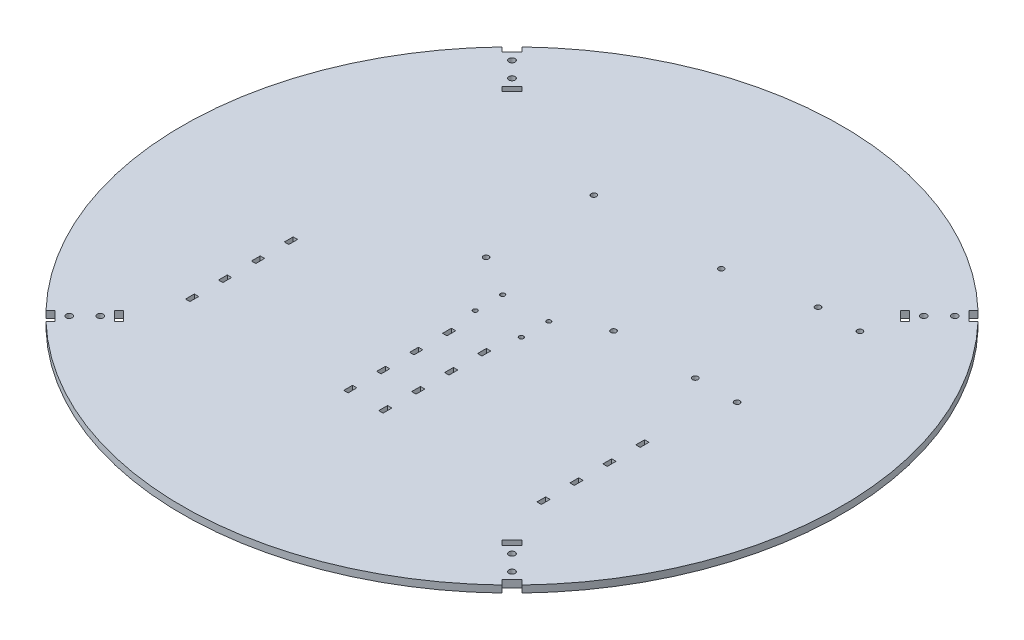
SolidWorks part; units mm, degrees
material "Acrylic (Medium-high impact)"
ref_plane "Front Plane" through (0, 0, 0) normal (0, 0, 1) x (1, 0, 0)
ref_plane "Top Plane" through (0, 0, 0) normal (0, 1, 0) x (1, 0, 0)
ref_plane "Right Plane" through (0, 0, 0) normal (1, 0, 0) x (0, 0, -1)
sketch "Sketch1" plane through (0, 0, 0) normal (0, 1, 0) x (1, 0, 0)
  line L0 (106.066, 212.132) -> (106.066, 0) construction
  line L5 (77.066, 172.2939) -> (135.066, 172.2939) construction
  line L6 (77.066, 172.2939) -> (77.066, 123.2939) construction
  line L7 (77.066, 123.2939) -> (135.066, 123.2939) construction
  line L8 (135.066, 172.2939) -> (135.066, 123.2939) construction
  line L9 (95.566, 99.816) -> (116.566, 99.816) construction
  line L10 (95.566, 99.816) -> (95.566, 112.316) construction
  line L11 (95.566, 112.316) -> (116.566, 112.316) construction
  line L12 (116.566, 99.816) -> (116.566, 112.316) construction
  line L13 (99.0985, 83.4399) -> (99.0985, 87.4399)
  line L14 (27.0985, 94.9399) -> (97.0985, 94.9399) construction
  line L15 (27.0985, 94.9399) -> (27.0985, 29.9399) construction
  line L16 (27.0985, 29.9399) -> (97.0985, 29.9399) construction
  line L17 (97.0985, 94.9399) -> (97.0985, 29.9399) construction
  line L18 (27.0985, 83.4399) -> (25.0985, 83.4399)
  line L19 (27.0985, 83.4399) -> (27.0985, 87.4399)
  line L20 (27.0985, 87.4399) -> (25.0985, 87.4399)
  line L21 (25.0985, 83.4399) -> (25.0985, 87.4399)
  line L22 (99.0985, 83.4399) -> (97.0985, 83.4399)
  line L23 (97.0985, 83.4399) -> (97.0985, 87.4399)
  line L24 (99.0985, 87.4399) -> (97.0985, 87.4399)
  line L25 (99.0985, 68.4399) -> (99.0985, 72.4399)
  line L26 (99.0985, 68.4399) -> (97.0985, 68.4399)
  line L27 (97.0985, 68.4399) -> (97.0985, 72.4399)
  line L28 (99.0985, 72.4399) -> (97.0985, 72.4399)
  line L29 (99.0985, 53.4399) -> (99.0985, 57.4399)
  line L30 (99.0985, 53.4399) -> (97.0985, 53.4399)
  line L31 (97.0985, 53.4399) -> (97.0985, 57.4399)
  line L32 (99.0985, 57.4399) -> (97.0985, 57.4399)
  line L33 (99.0985, 38.4399) -> (99.0985, 42.4399)
  line L34 (99.0985, 38.4399) -> (97.0985, 38.4399)
  line L35 (97.0985, 38.4399) -> (97.0985, 42.4399)
  line L36 (99.0985, 42.4399) -> (97.0985, 42.4399)
  line L37 (27.0985, 68.4399) -> (27.0985, 72.4399)
  line L38 (27.0985, 68.4399) -> (25.0985, 68.4399)
  line L39 (25.0985, 68.4399) -> (25.0985, 72.4399)
  line L40 (27.0985, 72.4399) -> (25.0985, 72.4399)
  line L41 (27.0985, 53.4399) -> (27.0985, 57.4399)
  line L42 (27.0985, 53.4399) -> (25.0985, 53.4399)
  line L43 (25.0985, 53.4399) -> (25.0985, 57.4399)
  line L44 (27.0985, 57.4399) -> (25.0985, 57.4399)
  line L45 (27.0985, 38.4399) -> (27.0985, 42.4399)
  line L46 (27.0985, 38.4399) -> (25.0985, 38.4399)
  line L47 (25.0985, 38.4399) -> (25.0985, 42.4399)
  line L48 (27.0985, 42.4399) -> (25.0985, 42.4399)
  line L49 (106.066, 112.316) -> (106.066, 99.816) construction
  line L50 (172.245, 123.2939) -> (172.245, 179.1739) construction
  line L51 (172.245, 123.2939) -> (191.295, 123.2939) construction
  line L52 (191.295, 123.2939) -> (191.295, 179.1739) construction
  line L53 (172.245, 179.1739) -> (191.295, 179.1739) construction
  line L54 (113.0335, 83.4399) -> (115.0335, 83.4399)
  line L55 (115.0335, 83.4399) -> (115.0335, 87.4399)
  line L56 (113.0335, 87.4399) -> (115.0335, 87.4399)
  line L57 (113.0335, 83.4399) -> (113.0335, 87.4399)
  line L58 (113.0335, 68.4399) -> (115.0335, 68.4399)
  line L59 (115.0335, 68.4399) -> (115.0335, 72.4399)
  line L60 (113.0335, 72.4399) -> (115.0335, 72.4399)
  line L61 (113.0335, 68.4399) -> (113.0335, 72.4399)
  line L62 (113.0335, 53.4399) -> (115.0335, 53.4399)
  line L63 (115.0335, 53.4399) -> (115.0335, 57.4399)
  line L64 (113.0335, 57.4399) -> (115.0335, 57.4399)
  line L65 (113.0335, 53.4399) -> (113.0335, 57.4399)
  line L66 (113.0335, 38.4399) -> (115.0335, 38.4399)
  line L67 (115.0335, 38.4399) -> (115.0335, 42.4399)
  line L68 (113.0335, 42.4399) -> (115.0335, 42.4399)
  line L69 (113.0335, 38.4399) -> (113.0335, 42.4399)
  line L70 (185.0335, 38.4399) -> (187.0335, 38.4399)
  line L71 (187.0335, 38.4399) -> (187.0335, 42.4399)
  line L72 (185.0335, 42.4399) -> (187.0335, 42.4399)
  line L73 (185.0335, 38.4399) -> (185.0335, 42.4399)
  line L74 (185.0335, 53.4399) -> (187.0335, 53.4399)
  line L75 (187.0335, 53.4399) -> (187.0335, 57.4399)
  line L76 (185.0335, 57.4399) -> (187.0335, 57.4399)
  line L77 (185.0335, 53.4399) -> (185.0335, 57.4399)
  line L78 (185.0335, 68.4399) -> (187.0335, 68.4399)
  line L79 (187.0335, 68.4399) -> (187.0335, 72.4399)
  line L80 (185.0335, 72.4399) -> (187.0335, 72.4399)
  line L81 (185.0335, 68.4399) -> (185.0335, 72.4399)
  line L82 (185.0335, 87.4399) -> (187.0335, 87.4399)
  line L83 (187.0335, 83.4399) -> (187.0335, 87.4399)
  line L84 (185.0335, 83.4399) -> (187.0335, 83.4399)
  line L85 (185.0335, 83.4399) -> (185.0335, 87.4399)
  circle A0 centre (77.066, 172.2939) radius 1.25
  circle A1 centre (135.066, 172.2939) radius 1.25
  circle A2 centre (77.066, 123.2939) radius 1.25
  circle A3 centre (135.066, 123.2939) radius 1.25
  circle A6 centre (95.566, 112.316) radius 1
  circle A7 centre (116.566, 112.316) radius 1
  circle A8 centre (116.566, 99.816) radius 1
  circle A9 centre (95.566, 99.816) radius 1
  circle A10 centre (172.245, 123.2939) radius 1.25
  circle A11 centre (172.245, 179.1739) radius 1.25
  circle A12 centre (191.295, 123.2939) radius 1.25
  circle A13 centre (191.295, 179.1739) radius 1.25
  circle A14 centre (106.066, 106.066) radius 150
  point P15 (106.066, 172.2939)
  point P78 (106.066, 106.066)
  point P92 (80, 80)
  dimension "D3" = 2.5
  dimension "D4" = 300
  dimension "D11" = 2
  dimension "D23" = 2.5
  dimension "D1" = 58
  dimension "D2" = 49
  dimension "D9" = 21
  dimension "D10" = 12.5
  dimension "D13" = 70
  dimension "D14" = 65
  dimension "D16" = 2
  dimension "D17" = 4
  dimension "D18" = 7.5
  dimension "D21" = 55.88
  dimension "D22" = 19.05
  dimension "D19" = 2
  dimension "D20" = 4
extrude "Boss-Extrude1" add sketch "Sketch1" along normal blind 3.175
sketch "Sketch2" plane through (0, 3.175, 0) normal (0, 1, 0) x (1, 0, 0)
  line L0 (15.4326, 192.2093) -> (13.3113, 194.3306) construction
  line L1 (13.3113, 194.3306) -> (17.8014, 198.8207) construction
  line L2 (17.8014, 198.8207) -> (19.9227, 196.6994) construction
  line L3 (19.9227, 196.6994) -> (15.4326, 192.2093) construction
  line L4 (-0.1237, 207.7656) -> (-2.2451, 209.887) construction
  line L5 (-2.2451, 209.887) -> (2.2451, 214.3771) construction
  line L6 (2.2451, 214.3771) -> (4.3664, 212.2558) construction
  line L7 (4.3664, 212.2558) -> (-0.1237, 207.7656) construction
  line L8 (15.4326, 192.2093) -> (13.3113, 194.3306)
  line L9 (13.3113, 194.3306) -> (17.8014, 198.8207)
  line L10 (17.8014, 198.8207) -> (19.9227, 196.6994)
  line L11 (19.9227, 196.6994) -> (15.4326, 192.2093)
  line L12 (-0.1237, 207.7656) -> (-2.2451, 209.887)
  line L13 (-2.2451, 209.887) -> (2.2451, 214.3771)
  line L14 (2.2451, 214.3771) -> (4.3664, 212.2558)
  line L15 (4.3664, 212.2558) -> (-0.1237, 207.7656)
  line L16 (106.066, 256.066) -> (106.066, -43.934) construction
  line L17 (192.2093, 196.6994) -> (194.3306, 198.8207)
  line L18 (194.3306, 198.8207) -> (198.8207, 194.3306)
  line L19 (198.8207, 194.3306) -> (196.6994, 192.2093)
  line L20 (196.6994, 192.2093) -> (192.2093, 196.6994)
  line L21 (207.7656, 212.2558) -> (209.887, 214.3771)
  line L22 (209.887, 214.3771) -> (214.3771, 209.887)
  line L23 (214.3771, 209.887) -> (212.2558, 207.7656)
  line L24 (212.2558, 207.7656) -> (207.7656, 212.2558)
  line L25 (196.6994, 19.9227) -> (198.8207, 17.8014)
  line L26 (198.8207, 17.8014) -> (194.3306, 13.3113)
  line L27 (194.3306, 13.3113) -> (192.2093, 15.4326)
  line L28 (192.2093, 15.4326) -> (196.6994, 19.9227)
  line L29 (212.2558, 4.3664) -> (214.3771, 2.2451)
  line L30 (214.3771, 2.2451) -> (209.887, -2.2451)
  line L31 (209.887, -2.2451) -> (207.7656, -0.1237)
  line L32 (207.7656, -0.1237) -> (212.2558, 4.3664)
  line L33 (19.9227, 15.4326) -> (17.8014, 13.3113)
  line L34 (17.8014, 13.3113) -> (13.3113, 17.8014)
  line L35 (13.3113, 17.8014) -> (15.4326, 19.9227)
  line L36 (15.4326, 19.9227) -> (19.9227, 15.4326)
  line L37 (4.3664, -0.1237) -> (2.2451, -2.2451)
  line L38 (2.2451, -2.2451) -> (-2.2451, 2.2451)
  line L39 (-2.2451, 2.2451) -> (-0.1237, 4.3664)
  line L40 (-0.1237, 4.3664) -> (4.3664, -0.1237)
  circle A0 centre (5.3033, 206.8287) radius 1.4224 construction
  circle A1 centre (12.3744, 199.7577) radius 1.4224 construction
  circle A2 centre (5.3033, 206.8287) radius 1.4224
  circle A3 centre (12.3744, 199.7577) radius 1.4224
  circle A4 centre (106.066, 106.066) radius 150 construction
  circle A5 centre (206.8287, 206.8287) radius 1.4224
  circle A6 centre (199.7577, 199.7577) radius 1.4224
  circle A7 centre (206.8287, 5.3033) radius 1.4224
  circle A8 centre (199.7577, 12.3744) radius 1.4224
  circle A9 centre (5.3033, 5.3033) radius 1.4224
  circle A10 centre (12.3744, 12.3744) radius 1.4224
  point P14 (106.066, 106.066)
  point P15 (106.066, 106.066)
  point P59 (106.066, 106.066)
  dimension "D1" = 4
extrude "Cut-Extrude1" cut sketch "Sketch2" against normal blind 10
equation "\"d\"=12.7"
